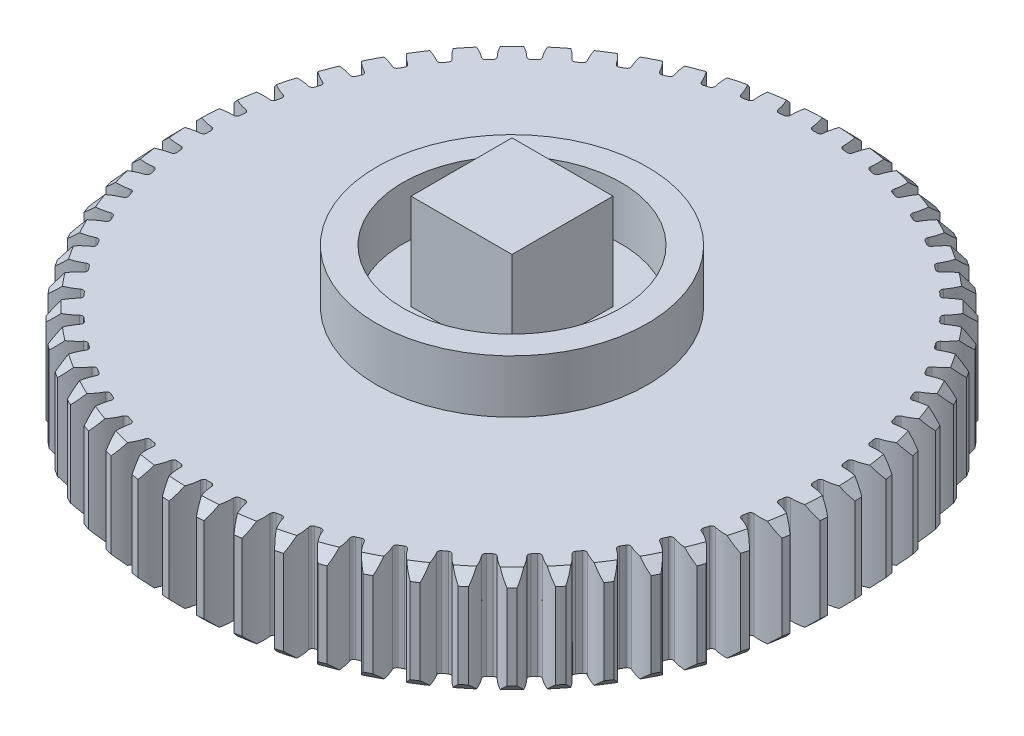
SolidWorks part; units mm, degrees
ref_plane "Front Plane" through (0, 0, 0) normal (0, 0, 1) x (1, 0, 0)
ref_plane "Top Plane" through (0, 0, 0) normal (0, 1, 0) x (1, 0, 0)
ref_plane "Right Plane" through (0, 0, 0) normal (1, 0, 0) x (0, 0, -1)
sketch "Sketch1" plane through (0, 0, 0) normal (0, 1, 0) x (1, 0, 0)
  circle A0 centre (0, 0) radius 30 construction
  circle A1 centre (0, 0) radius 31
  dimension "D1" = 60
  dimension "D2" = 62
extrude "Boss-Extrude1" add sketch "Sketch1" along normal mid plane 10
sketch "Sketch2" plane through (0, 0, 0) normal (0, 1, 0) x (1, 0, 0)
  line L0 (0, 31) -> (0, 0) construction
  line L1 (0, 0) -> (1.6224, 30.9575) construction
  line L2 (0, 0) -> (3.2404, 30.8302) construction
  line L3 (-0.5081, 28.4955) -> (0, 0) construction
  line L4 (-0.7853, 29.9897) -> (0.7853, 29.9897) construction
  line L5 (0.7853, 29.9897) -> (2.3538, 29.9075) construction
  line L6 (-1.1453, 30.9788) -> (0, 27.8321) construction
  circle A0 centre (0, 0) radius 29 construction
  circle A2 centre (0, 0) radius 31 construction
  arc A3 (-1.2837, 30.9734) -> (-0.5081, 28.4955) centre (-5.1165, 28.4133) cw
  arc A4 (1.2837, 30.9734) -> (0.5081, 28.4955) centre (5.1165, 28.4133) ccw
  circle A5 centre (0, 0) radius 30 construction
  arc A6 (0.5081, 28.4955) -> (-0.5081, 28.4955) centre (0, 0) ccw
  arc A7 (-1.2837, 30.9734) -> (1.2837, 30.9734) centre (0, 0) cw
  dimension "D1" = 6
  dimension "D2" = 3
  dimension "D4" = 2
  dimension "D5" = 20
  dimension "D3" = 0.5
extrude "Cut-Extrude4" cut sketch "Sketch2" against normal through all both and the other way through all
fillet "Fillet1" radius 0.3 2 edges at (0.5081, 0, -28.4955) (-0.5081, 0, -28.4955)
chamfer "Chamfer1" distance 1 angle 45 2 edges at (0, 5, 31) (0, -5, 31)
pattern_circular "CirPattern1" count 60 over 360 about axis through (0, 0, 0) along (0, 1, 0) of "Fillet1", "Cut-Extrude4"
sketch "Sketch3" plane through (0, 5, 0) normal (0, 1, 0) x (1, 0, 0)
  circle A0 centre (0, 0) radius 10.25
  circle A1 centre (0, 0) radius 12.75
  dimension "D1" = 20.5
  dimension "D2" = 2.5
sketch "Sketch5" plane through (0, 5, 0) normal (0, 1, 0) x (1, 0, 0)
  line L1 (-4.75, 4.75) -> (4.75, 4.75)
  line L2 (-4.75, 4.75) -> (-4.75, -4.75)
  line L3 (-4.75, -4.75) -> (4.75, -4.75)
  line L4 (4.75, 4.75) -> (4.75, -4.75)
  line L5 (-4.75, 4.75) -> (4.75, -4.75) construction
  line L6 (-4.75, -4.75) -> (4.75, 4.75) construction
  point P0 (0, 0)
  dimension "D1" = 9.5
  dimension "D2" = 9.5
extrude "Boss-Extrude3" add sketch "Sketch3" along normal blind 5
extrude "Boss-Extrude4" add sketch "Sketch5" along normal blind 9
sketch "Sketch6" plane through (0, -5, 0) normal (0, -1, 0) x (1, 0, 0)
  circle A0 centre (0, 0) radius 7.5
  dimension "D1" = 15
extrude "Boss-Extrude5" add sketch "Sketch6" along normal blind 10
equation "\"D1@Sketch1\" = \"Module\" * \"Number of Teeth\""
equation "\"D2@Sketch1\" = ( \"Number of Teeth\" + 2 ) * \"Module\""
equation "\"D1@Sketch2\" = 360 / \"Number of Teeth\""
equation "\"D2@Sketch2\" = 180 / \"Number of Teeth\""
equation "\"D4@Sketch2\" = \"Module\" * 2"
equation "\"D5@Sketch2\"= \"Pressure Angle\""
equation "\"D1@Fillet1\" = 0.3 * \"Module\""
equation "\"D1@CirPattern1\" = \"Number of Teeth\""
equation "\"D1@Chamfer1\" = \"Module\""
